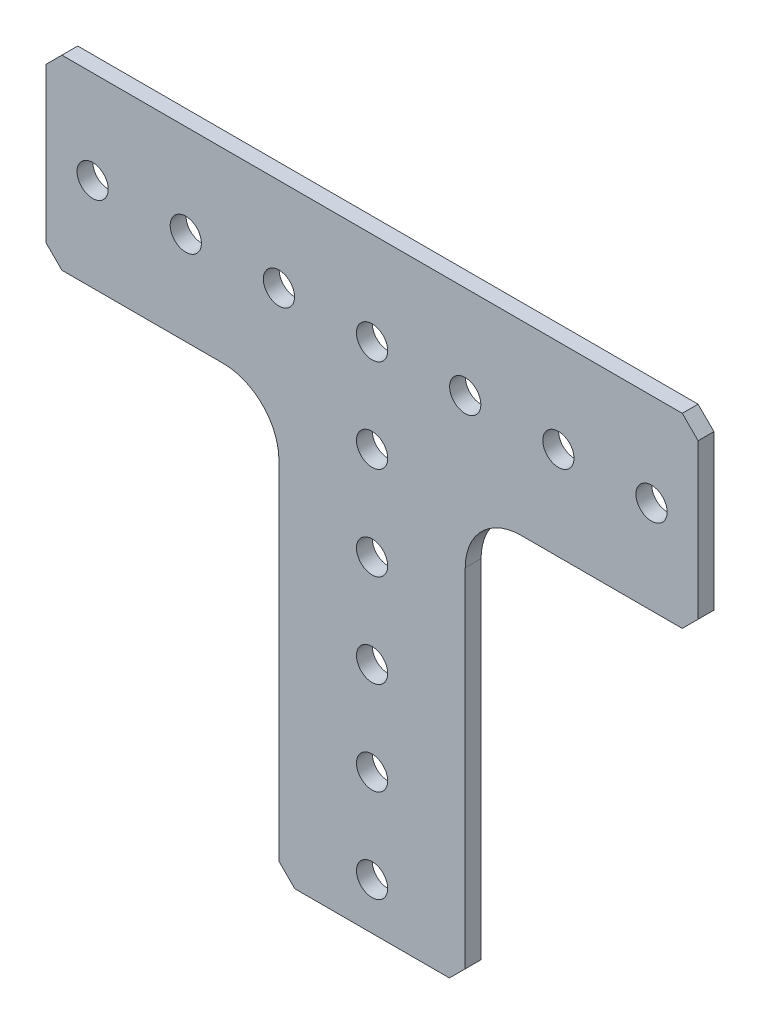
SolidWorks part; units mm, degrees
ref_plane "Front Plane" through (0, 0, 0) normal (0, 0, 1) x (1, 0, 0)
ref_plane "Top Plane" through (0, 0, 0) normal (0, 1, 0) x (1, 0, 0)
ref_plane "Right Plane" through (0, 0, 0) normal (1, 0, 0) x (0, 0, -1)
sketch "Sketch1" plane through (0, 0, 0) normal (0, 0, 1) x (1, 0, 0)
  line L0 (-29.915, 40.5708) -> (-61.665, 40.5708)
  line L1 (-29.915, 40.5708) -> (-4.515, 40.5708)
  line L2 (-29.915, 40.5708) -> (-29.915, -16.5792)
  line L3 (-29.915, -16.5792) -> (-4.515, -16.5792)
  line L4 (-4.515, 40.5708) -> (-4.515, -16.5792)
  line L5 (-61.665, 40.5708) -> (-61.665, 65.9708)
  line L6 (-61.665, 65.9708) -> (27.235, 65.9708)
  line L7 (27.235, 65.9708) -> (27.235, 40.5708)
  line L8 (27.235, 40.5708) -> (-4.515, 40.5708)
  dimension "D1" = 57.15
  dimension "D2" = 25.4
  dimension "D3" = 31.75
  dimension "D4" = 25.4
  dimension "D5" = 88.9
  dimension "D6" = 25.4
extrude "Boss-Extrude1" add sketch "Sketch1" along normal blind 2.159 contours L8 L7 L6 L5 L0 L1 | L4 L1 L2 L3
fillet "Fillet1" radius 7.62 2 edges at (-4.515, 40.5708, 1.0795) (-29.915, 40.5708, 1.0795)
chamfer "Chamfer1" distance 2.159 6 edges at (-61.665, 65.9708, 1.0795) (-61.665, 40.5708, 1.0795) (-29.915, -16.5792, 1.0795) (-4.515, -16.5792, 1.0795) (27.235, 65.9708, 1.0795) (27.235, 40.5708, 1.0795)
sketch "Sketch2" plane through (0, 0, 2.159) normal (0, 0, 1) x (1, 0, 0)
  line L0 (-17.215, -16.5792) -> (-17.215, -10.2292)
  line L1 (-27.756, -16.5792) -> (-6.674, -16.5792) construction
  line L2 (-17.215, -10.2292) -> (-17.215, 2.4708)
  line L3 (-17.215, 2.4708) -> (-17.215, 15.1708)
  line L4 (-17.215, 15.1708) -> (-17.215, 27.8708)
  line L5 (-17.215, 27.8708) -> (-17.215, 40.5708)
  line L6 (-17.215, 40.5708) -> (-17.215, 53.2708)
  line L7 (-17.215, 53.2708) -> (-4.515, 53.2708)
  line L8 (-4.515, 53.2708) -> (8.185, 53.2708)
  line L9 (8.185, 53.2708) -> (20.885, 53.2708)
  line L10 (-29.915, 53.2708) -> (-17.215, 53.2708)
  line L11 (-42.615, 53.2708) -> (-29.915, 53.2708)
  line L12 (-55.315, 53.2708) -> (-42.615, 53.2708)
  point P5 (-17.215, -10.2292)
  point P7 (-17.215, 2.4708)
  point P10 (-4.515, 53.2708)
  dimension "D1" = 6.35
  dimension "D2" = 12.7
  dimension "D3" = 5
  dimension "D4" = 12.7
  dimension "D5" = 3
  dimension "D6" = 4
hole_wizard "1/4 (0.25) Diameter Hole1" positions "Sketch3" profile "Sketch4" hole size "1/4" standard "ANSI Inch"
sketch "Sketch3" plane through (0, 0, 2.159) normal (0, 0, 1) x (1, 0, 0)
  point P0 (-55.315, 53.2708)
  point P3 (-42.615, 53.2708)
  point P6 (-29.915, 53.2708)
  point P9 (-17.215, 53.2708)
  point P12 (-4.515, 53.2708)
  point P15 (8.185, 53.2708)
  point P18 (20.885, 53.2708)
  point P21 (-17.215, 40.5708)
  point P24 (-17.215, 27.8708)
  point P27 (-17.215, 15.1708)
  point P30 (-17.215, 2.4708)
  point P33 (-17.215, -10.2292)
sketch "Sketch4" plane through (-55.315, 53.2708, 2.159) normal (1, 0, 0) x (0, -1, 0)
  line L0 (0, 0) -> (0, 2.158)
  line L1 (0, 2.158) -> (2.1272, 2.158)
  line L2 (2.1272, 2.158) -> (2.1272, 0)
  line L5 (2.1272, 0) -> (0, 0)
  line L10 (0, 2.158) -> (-2.1273, 2.158) construction
  line L11 (0, -6.35) -> (0, 107.95) construction
  dimension "Hole Dia." = 4.2545
  dimension "Hole Depth" = 2.158
  dimension "Drill Angle" = 180
